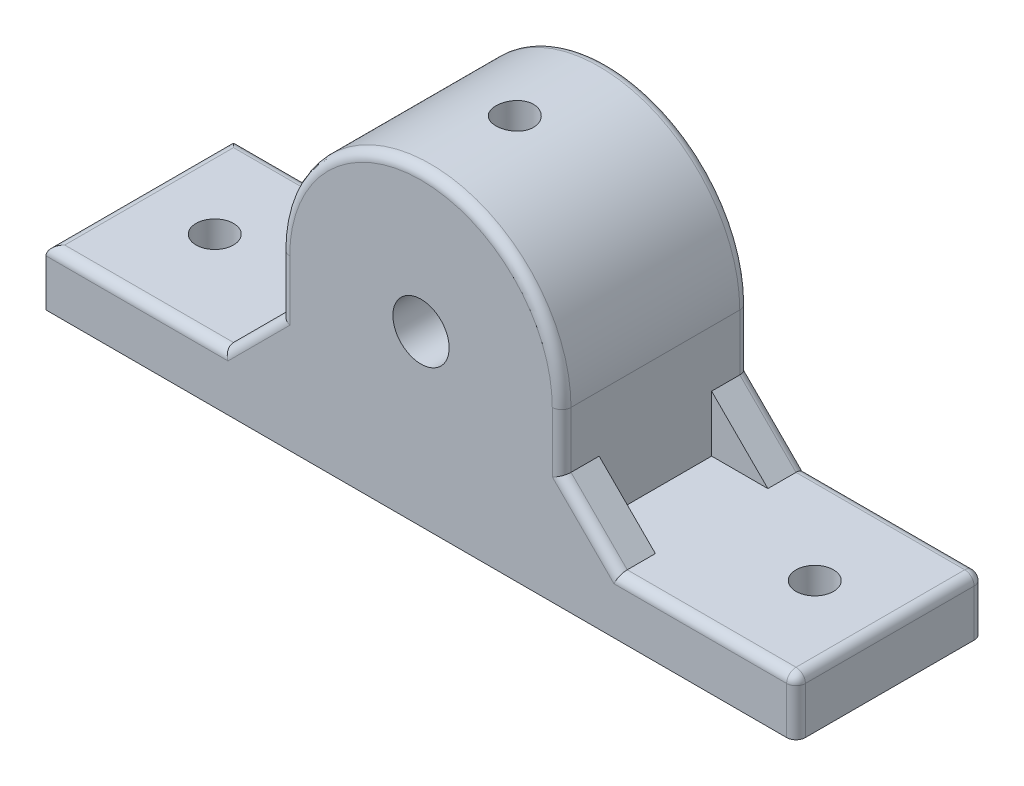
SolidWorks part; units mm, degrees
ref_plane "Plan de face" through (0, 0, 0) normal (0, 0, 1) x (1, 0, 0)
ref_plane "Plan de dessus" through (0, 0, 0) normal (0, 1, 0) x (1, 0, 0)
ref_plane "Plan de droite" through (0, 0, 0) normal (1, 0, 0) x (0, 0, -1)
sketch "Esquisse1" plane through (0, 0, 0) normal (0, 0, 1) x (1, 0, 0)
  line L0 (-20, 0) -> (20, 0)
  line L1 (0, 0) -> (0, 6) construction
  line L2 (-20, 0) -> (-20, 3)
  line L3 (-20, 3) -> (-7.5, 3)
  line L4 (-7.5, 3) -> (-7.5, 9)
  line L5 (20, 0) -> (20, 3)
  line L6 (20, 3) -> (7.5, 3)
  line L7 (7.5, 3) -> (7.5, 9)
  arc A0 (7.5, 9) -> (-7.5, 9) centre (0, 9) ccw
  dimension "D1" = 3
  dimension "D2" = 40
  dimension "D3" = 15
  dimension "D4" = 9
extrude "Boss.-Extru.1" add sketch "Esquisse1" along normal mid plane 10
sketch "Esquisse2" plane through (0, 0, 5) normal (0, 0, 1) x (1, 0, 0)
  line L0 (-10.5, 3) -> (-7.5, 6)
  line L1 (-7.5, 3) -> (-20, 3) construction
  line L2 (-7.5, 9) -> (-7.5, 3) construction
  line L3 (-7.5, 6) -> (-7.5, 3)
  line L4 (-7.5, 3) -> (-10.5, 3)
  dimension "D1" = 45
  dimension "D2" = 3
extrude "Boss.-Extru.2" add sketch "Esquisse2" against normal blind 2 contours L0 L3 L4
mirror "Symétrie1" about plane through (0, 0, 0) normal (0, 0, 1) of "Boss.-Extru.2"
mirror "Symétrie2" about plane through (0, 0, 0) normal (1, 0, 0) of "Symétrie1", "Boss.-Extru.2"
fillet "Congé1" radius 0.5 18 edges at (-9, 4.5, -5) (-7.5, 7.5, -5) (-20, 3, 0) (-15.25, 3, -5) (7.5, 7.5, -5) (9, 4.5, -5) (15.25, 3, -5) (20, 1.5, -5) (20, 3, 0) (20, 1.5, 5) (15.25, 3, 5) (9, 4.5, 5) (-9, 4.5, 5) (-15.25, 3, 5) (-7.5, 7.5, 5) (7.5, 7.5, 5) (0, 16.5, -5) (0, 16.5, 5)
sketch "Esquisse3" plane through (0, 3, 0) normal (0, 1, 0) x (1, 0, 0)
  line L0 (-20, -5) -> (-20, 5) construction
  line L1 (0, 0) -> (0, 8.6742) construction
  circle A0 centre (-16, 0) radius 1
  circle A1 centre (16, 0) radius 1
  dimension "D1" = 2
  dimension "D2" = 4
sketch "Esquisse4" plane through (0, 0, 5) normal (0, 0, 1) x (1, 0, 0)
  line L0 (-20, 0) -> (19.5, 0) construction
  circle A0 centre (0, 9) radius 1.5
  dimension "D1" = 3
  dimension "D2" = 9
extrude "Enlèv. mat.-Extru.2" cut sketch "Esquisse4" against normal through all both and the other way through all
ref_plane "Plan1" through (0, 16.5, 0) normal (0, 1, 0) x (1, 0, 0)
sketch "Esquisse5" plane through (0, 16.5, 0) normal (0, 1, 0) x (1, 0, 0)
  circle A0 centre (0, 0) radius 1
  dimension "D1" = 2
extrude "Enlèv. mat.-Extru.3" cut sketch "Esquisse5" against normal blind 7
extrude "Enlèv. mat.-Extru.1" cut sketch "Esquisse3" against normal through all both and the other way through all
